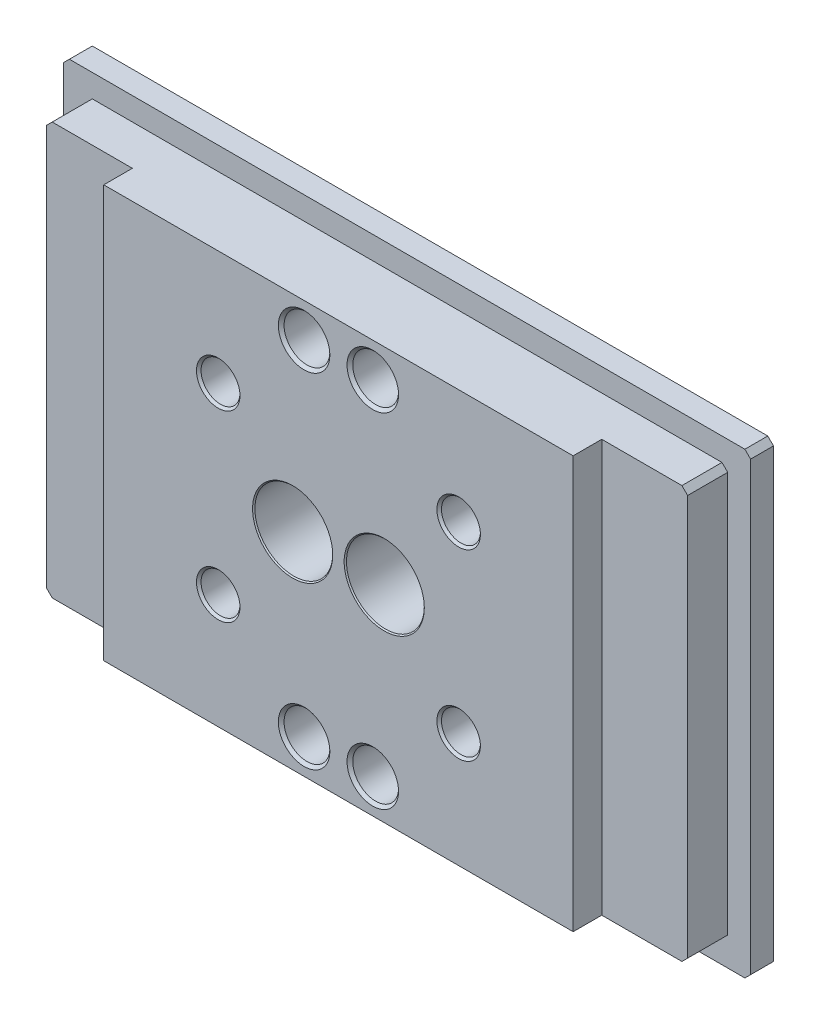
SolidWorks part; units mm, degrees
material "Акрил (Средняя-высокая ударопрочность)"
ref_plane "Front" through (0, 0, 0) normal (0, 0, 1) x (1, 0, 0)
ref_plane "Top" through (0, 0, 0) normal (0, 1, 0) x (1, 0, 0)
ref_plane "Right" through (0, 0, 0) normal (1, 0, 0) x (0, 0, -1)
sketch "Эскиз1" plane through (0, 0, 0) normal (0, 0, 1) x (1, 0, 0)
  line L1 (-30, -20) -> (30, -20)
  line L2 (-30, -20) -> (-30, 20)
  line L3 (-30, 20) -> (30, 20)
  line L4 (30, -20) -> (30, 20)
  line L5 (-30, -20) -> (30, 20) construction
  line L6 (-30, 20) -> (30, -20) construction
  point P0 (0, 0)
  dimension "D1" = 40
  dimension "D2" = 60
extrude "Бобышка-Вытянуть1" add sketch "Эскиз1" along normal blind 8
sketch "Эскиз2" plane through (0, 0, 8) normal (0, 0, 1) x (1, 0, 0)
  line L1 (-28, -18) -> (28, -18)
  line L2 (-28, -18) -> (-28, 18)
  line L3 (-28, 18) -> (28, 18)
  line L4 (28, -18) -> (28, 18)
  line L5 (-28, -18) -> (28, 18) construction
  line L6 (-28, 18) -> (28, -18) construction
  point P0 (0, 0)
  dimension "D1" = 36
  dimension "D2" = 56
extrude "Вырез-Вытянуть1" cut sketch "Эскиз2" against normal offset from surface (6 mm away) 2 flip side to cut up to face at (0, 0, 0)
chamfer "Фаска1" distance 0.5 angle 45 8 edges at (28, 18, 5) (28, -18, 5) (-28, -18, 5) (-28, 18, 5) (-30, -20, 1) (-30, 20, 1) (30, 20, 1) (30, -20, 1)
hole_wizard "Диаметр отверстия Ø4.0 (4)1" positions "Эскиз4" profile "Эскиз3" hole size "Ø4.0" standard "DIN"
sketch "Эскиз4" plane through (0, 0, 8) normal (0, 0, 1) x (1, 0, 0)
  point P0 (-3, -15)
  point P1 (3, -15)
  point P3 (3, 15)
  point P5 (-3, 15)
  dimension "D1" = 6
  dimension "D2" = 30
  dimension "D3" = 15
  dimension "D4" = 3
sketch "Эскиз3" plane through (-3, -15, 8) normal (1, 0, 0) x (0, -1, 0)
  line L0 (0, 0) -> (0, 5.7017)
  line L1 (0, 5.7017) -> (2, 4.5)
  line L2 (2, 4.5) -> (2, 0.25)
  line L3 (2, 0.25) -> (2.25, 0)
  line L5 (2.25, 0) -> (0, 0)
  line L6 (-2, 0.25) -> (-2.25, 0) construction
  line L10 (0, 5.7017) -> (-2, 4.5) construction
  line L11 (0, -6.35) -> (0, 107.95) construction
  dimension "Диаметр отверстия" = 4
  dimension "Глубина отверстия" = 4.5
  dimension "Диаметр передней зенковки" = 4.5
  dimension "Угол передней зенковки" = 90
  dimension "Угол заточки сверла" = 118
hole_wizard "Цековка для винта с внутренним шестигранником M31" positions "Эскиз6" profile "Эскиз5" counterbore size "M3" standard "Ansi (метрические)" end condition through all
sketch "Эскиз6" plane through (0, 0, 0) normal (0, 0, -1) x (-1, 0, 0)
  point P0 (-10.5, 8)
  point P1 (10.5, 8)
  point P3 (10.5, -8)
  point P5 (-10.5, -8)
  dimension "D1" = 21
  dimension "D2" = 10.5
  dimension "D3" = 8
  dimension "D4" = 16
sketch "Эскиз5" plane through (10.5, 8, 0) normal (1, 0, 0) x (0, 1, 0)
  line L0 (0, 0) -> (0, 8)
  line L1 (1.7, 7.8) -> (1.9, 8)
  line L2 (1.7, 7.8) -> (1.7, 3.7)
  line L3 (1.7, 3.7) -> (1.9, 3.5)
  line L4 (1.9, 3.5) -> (3.25, 3.5)
  line L5 (3.25, 3.5) -> (3.25, 0.25)
  line L6 (3.25, 0.25) -> (3.5, 0)
  line L7 (3.5, 0) -> (0, 0)
  line L8 (-3.25, 0.25) -> (-3.5, 0) construction
  line L9 (-1.7, 3.7) -> (-1.9, 3.5) construction
  line L11 (0, -6.35) -> (0, 107.95) construction
  line L12 (1.9, 8) -> (0, 8)
  line L13 (-1.7, 7.8) -> (-1.9, 8) construction
  dimension "Диаметр сквозного отверстия" = 3.4
  dimension "Глубина сквозного отверстия" = 8
  dimension "Диаметр цековки" = 6.5
  dimension "Глубина цековки" = 3.5
  dimension "Диаметр передней зенковки" = 7
  dimension "Угол передней зенковки" = 90
  dimension "Диаметр средней зенковки" = 3.8
  dimension "Угол средней зенковки" = 90
  dimension "Диаметр задней зенковки" = 3.8
  dimension "Угол задней зенковки" = 90
sketch "Эскиз7" plane through (0, 0, 0) normal (0, 1, 0) x (1, 0, 0)
  line L0 (28, -5.5) -> (20.5, -5.5)
  line L1 (28, -8) -> (28, -2) construction
  line L2 (20.5, -5.5) -> (20.5, -8)
  line L3 (-27.5, -8) -> (27.5, -8) construction
  line L4 (-28, -5.5) -> (-20.5, -5.5)
  line L5 (-28, -2) -> (-28, -8) construction
  line L6 (-20.5, -5.5) -> (-20.5, -8)
  line L7 (28, -5.5) -> (28, -8)
  line L8 (28, -8) -> (20.5, -8)
  line L9 (-20.5, -8) -> (-28, -8)
  line L10 (-28, -8) -> (-28, -5.5)
  dimension "D1" = 7.5
  dimension "D2" = 2.5
extrude "Вырез-Вытянуть2" cut sketch "Эскиз7" against normal through all and the other way through all contours L8 L7 L0 L2 | L10 L9 L6 L4
hole_wizard "Диаметр отверстия Ø6.8 (6.8)1" positions "Эскиз9" profile "Эскиз8" hole size "Ø6.8" standard "Ansi (метрические)"
sketch "Эскиз9" plane through (0, 0, 8) normal (0, 0, 1) x (1, 0, 0)
  point P0 (4, 0)
  point P1 (-4, 0)
  dimension "D1" = 4
  dimension "D2" = 8
sketch "Эскиз8" plane through (4, 0, 8) normal (1, 0, 0) x (0, -1, 0)
  line L0 (0, 0) -> (0, 7.0429)
  line L1 (0, 7.0429) -> (3.4, 5)
  line L2 (3.4, 5) -> (3.4, 0.1)
  line L3 (3.4, 0.1) -> (3.5, 0)
  line L5 (3.5, 0) -> (0, 0)
  line L6 (-3.4, 0.1) -> (-3.5, 0) construction
  line L10 (0, 7.0429) -> (-3.4, 5) construction
  line L11 (0, -6.35) -> (0, 107.95) construction
  dimension "Диаметр отверстия" = 6.8
  dimension "Глубина отверстия" = 5
  dimension "Диаметр передней зенковки" = 7
  dimension "Угол передней зенковки" = 90
  dimension "Угол заточки сверла" = 118
